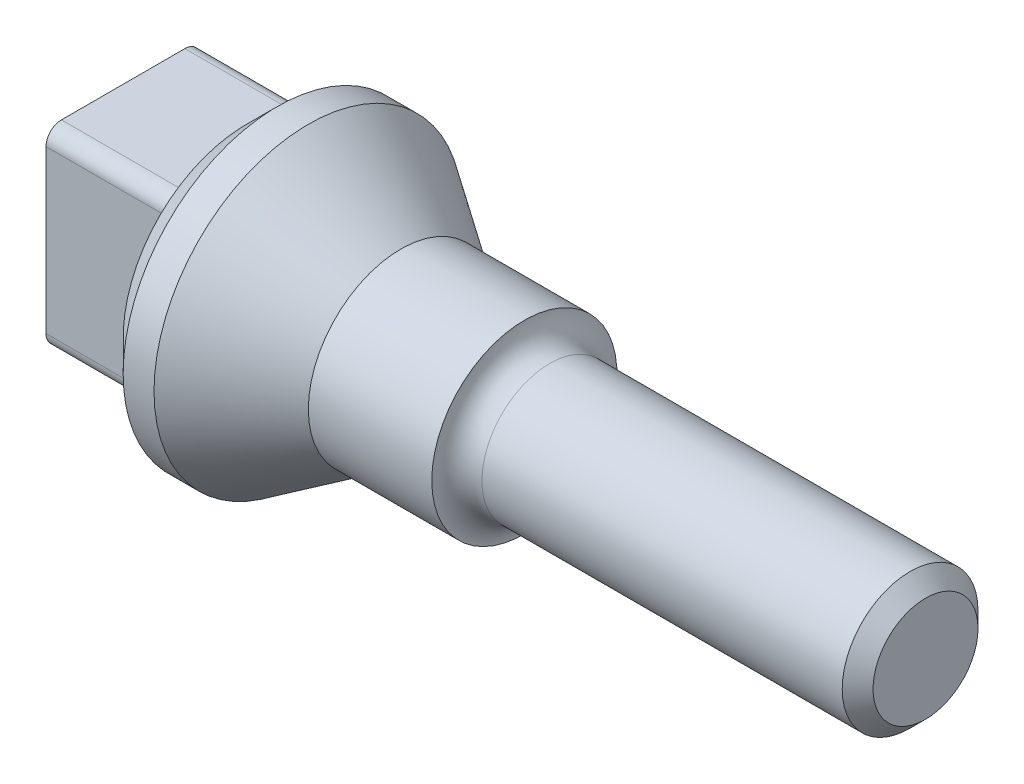
SolidWorks part; units mm, degrees
ref_plane "Front Plane" through (0, 0, 0) normal (0, 0, 1) x (1, 0, 0)
ref_plane "Top Plane" through (0, 0, 0) normal (0, 1, 0) x (1, 0, 0)
ref_plane "Right Plane" through (0, 0, 0) normal (1, 0, 0) x (0, 0, -1)
sketch "Sketch1" plane through (0, 0, 0) normal (0, 0, 1) x (1, 0, 0)
  line L0 (0, 0) -> (220, 0) construction
  line L1 (0, 0) -> (0, -40)
  line L2 (0, -40) -> (10, -50)
  line L3 (10, -50) -> (10, 0)
  line L4 (10, -50) -> (20, -50)
  line L5 (20, -50) -> (20, 0)
  line L6 (20, -50) -> (50, -30)
  line L7 (50, -30) -> (50, 0)
  line L8 (50, -30) -> (90, -30)
  line L9 (90, -30) -> (90, 0)
  line L10 (98.233, 0) -> (98.233, -22)
  line L11 (98.233, -22) -> (220, -22)
  line L12 (220, -22) -> (220, 0)
  arc A0 (98.233, -22) -> (90, -30) centre (98.233, -30.2364) ccw
  dimension "D1" = 220
  dimension "D2" = 40
  dimension "D3" = 10
  dimension "D4" = 50
  dimension "D5" = 10
  dimension "D6" = 30
  dimension "D7" = 30
  dimension "D8" = 40
  dimension "D9" = 22
revolve "Revolve1" add sketch "Sketch1" angle 360 about L0
sketch "Sketch2" plane through (0, 0, 0) normal (-1, 0, 0) x (0, 0, 1)
  line L1 (-25, -31.225) -> (25, -31.225)
  line L2 (-25, -31.225) -> (-25, 31.225)
  line L3 (-25, 31.225) -> (25, 31.225)
  line L4 (25, -31.225) -> (25, 31.225)
  line L5 (-25, -31.225) -> (25, 31.225) construction
  line L6 (-25, 31.225) -> (25, -31.225) construction
  circle A0 centre (0, 0) radius 40 construction
  point P0 (0, 0)
  dimension "D1" = 50
extrude "Boss-Extrude1" add sketch "Sketch2" along normal blind 40
fillet "Fillet2" radius 5 1 edges at (-20, 31.225, 25)
fillet "Fillet3" radius 5 3 edges at (-20, 31.225, -25) (-20, -31.225, -25) (-20, -31.225, 25)
chamfer "Chamfer1" distance 5 angle 45 1 edges at (220, 0, 22)
